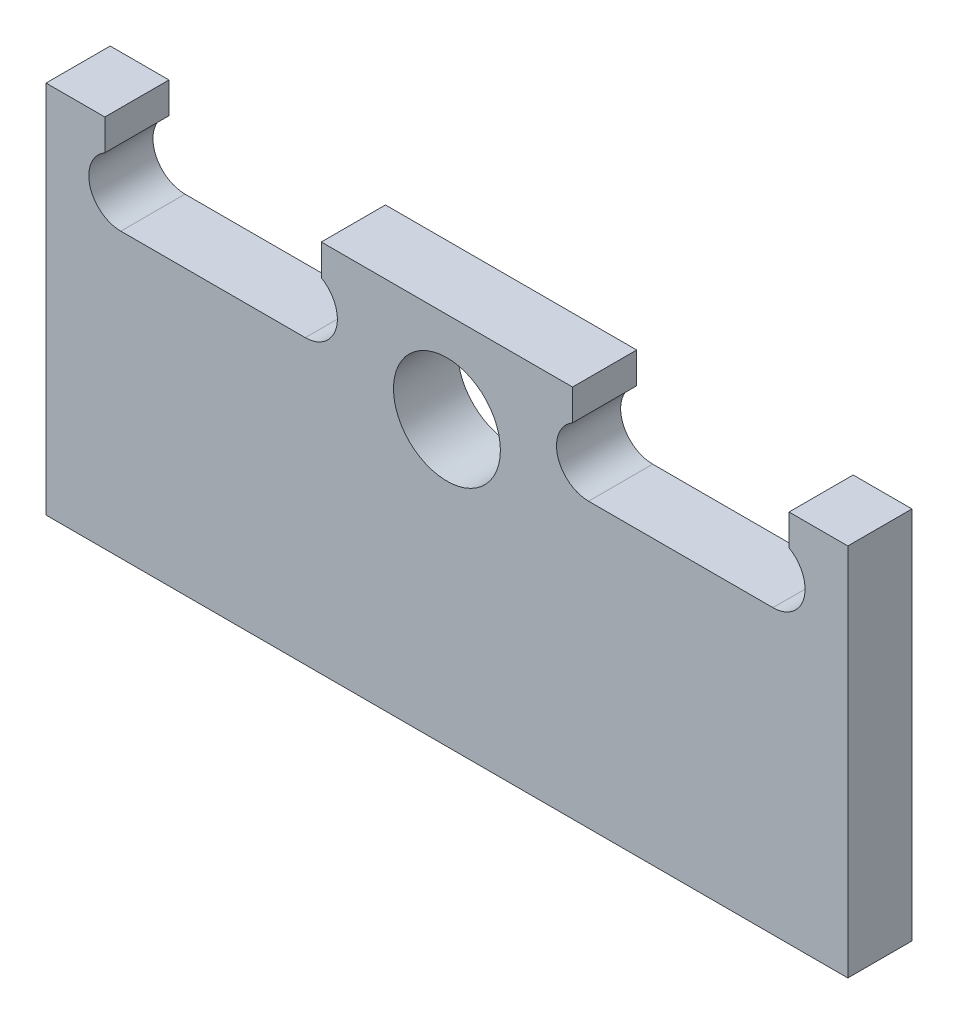
SolidWorks part; units mm, degrees
ref_plane "Alzado" through (0, 0, 0) normal (0, 0, 1) x (1, 0, 0)
ref_plane "Planta" through (0, 0, 0) normal (0, 1, 0) x (1, 0, 0)
ref_plane "Vista lateral" through (0, 0, 0) normal (1, 0, 0) x (0, 0, -1)
sketch "Croquis1" plane through (0, 0, 0) normal (0, 0, 1) x (1, 0, 0)
  line L0 (0, 0) -> (0, 70)
  line L1 (0, 70) -> (11, 70)
  line L2 (150, 70) -> (150, 0)
  line L3 (150, 0) -> (0, 0)
  line L4 (0, 59) -> (14, 59) construction
  line L5 (14, 59) -> (14, 70) construction
  line L6 (48.5, 53) -> (14, 53)
  line L7 (75, 0) -> (75, 70) construction
  line L8 (11, 70) -> (11, 64.1962)
  line L9 (51.5, 70) -> (51.5, 64.1962)
  line L10 (51.5, 70) -> (98.5, 70)
  line L11 (139, 70) -> (139, 64.1962)
  line L12 (98.5, 70) -> (98.5, 64.1962)
  line L13 (101.5, 53) -> (136, 53)
  line L14 (139, 70) -> (150, 70)
  arc A0 (11, 64.1962) -> (14, 53) centre (14, 59) ccw
  arc A1 (48.5, 53) -> (51.5, 64.1962) centre (48.5, 59) ccw
  arc A2 (101.5, 53) -> (98.5, 64.1962) centre (101.5, 59) cw
  arc A3 (139, 64.1962) -> (136, 53) centre (136, 59) cw
  circle A4 centre (75, 53) radius 10
  dimension "D5" = 34.5
  dimension "D9" = 17
  dimension "D1" = 70
  dimension "D2" = 150
  dimension "D3" = 14
  dimension "D4" = 11
  dimension "D6" = 11
  dimension "D7" = 40.5
  dimension "D8" = 70
extrude "Saliente-Extruir1" add sketch "Croquis1" along normal blind 12
